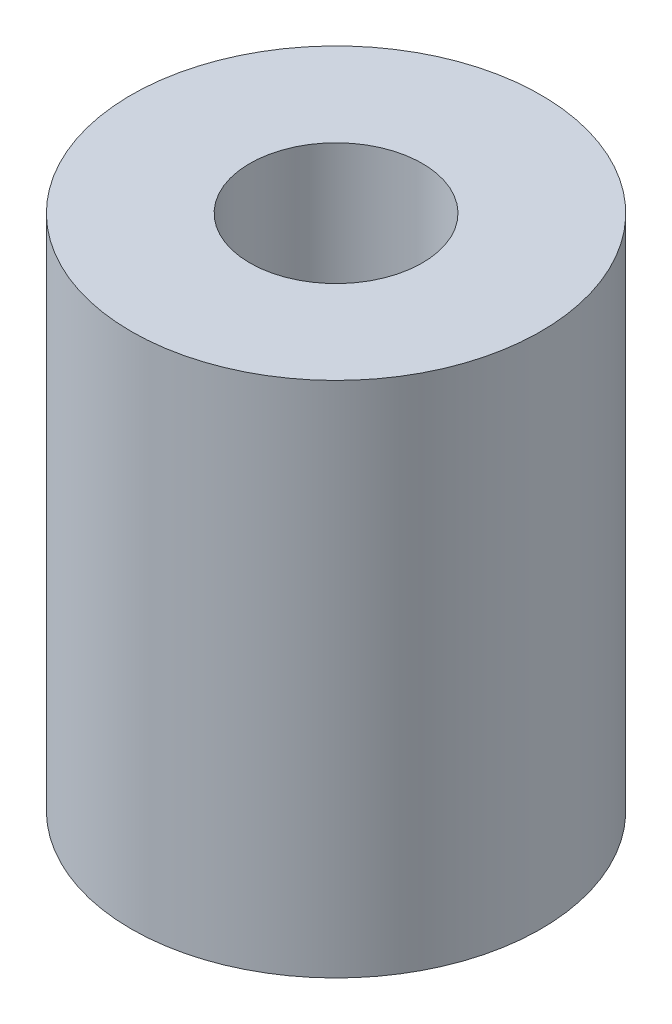
SolidWorks part; units mm, degrees
ref_plane "Front Plane" through (0, 0, 0) normal (0, 0, 1) x (1, 0, 0)
ref_plane "Top Plane" through (0, 0, 0) normal (0, 1, 0) x (1, 0, 0)
ref_plane "Right Plane" through (0, 0, 0) normal (1, 0, 0) x (0, 0, -1)
sketch "Sketch1" plane through (0, 0, 0) normal (0, 1, 0) x (1, 0, 0)
  circle A0 centre (0, 0) radius 9.5
  dimension "D1" = 19
extrude "Boss-Extrude1" add sketch "Sketch1" along normal blind 24
sketch "Sketch2" plane through (0, 24, 0) normal (0, 1, 0) x (1, 0, 0)
  circle A0 centre (0, 0) radius 4
  dimension "D1" = 8
extrude "Cut-Extrude1" cut sketch "Sketch2" against normal blind 12
sketch "Sketch3" plane through (0, 0, 0) normal (0, -1, 0) x (1, 0, 0)
  circle A0 centre (0, 0) radius 2.5
extrude "Cut-Extrude2" cut sketch "Sketch3" against normal blind 12
